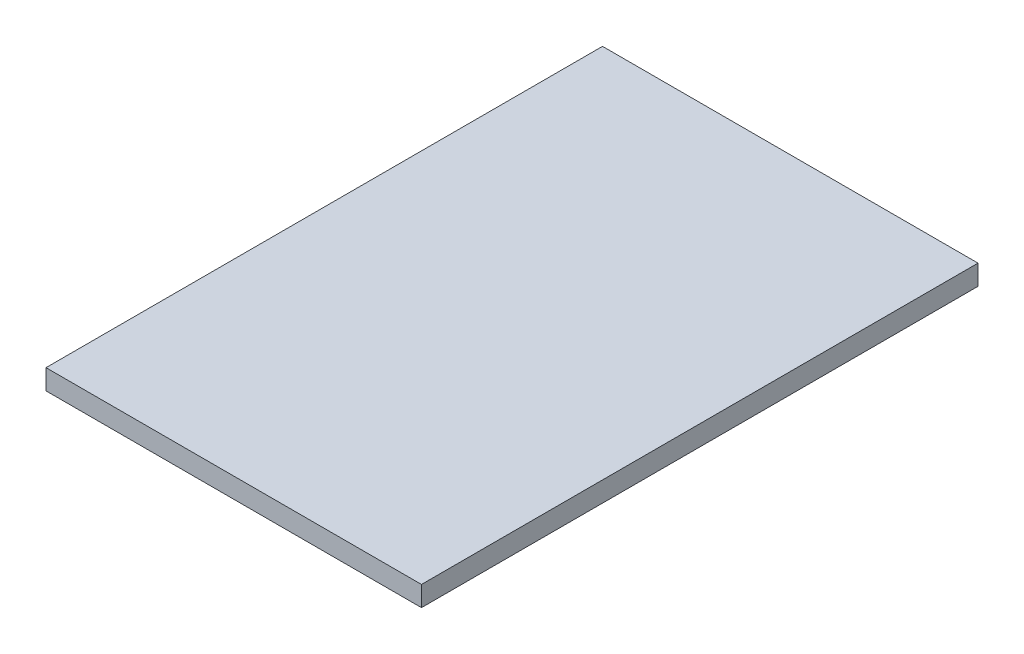
SolidWorks part; units mm, degrees
material "Balsa"
ref_plane "Front Plane" through (0, 0, 0) normal (0, 0, 1) x (1, 0, 0)
ref_plane "Top Plane" through (0, 0, 0) normal (0, 1, 0) x (1, 0, 0)
ref_plane "Right Plane" through (0, 0, 0) normal (1, 0, 0) x (0, 0, -1)
sketch "Sketch1" plane through (0, 0, 0) normal (0, 1, 0) x (1, 0, 0)
  line L1 (-88.9, -131.7625) -> (88.9, -131.7625)
  line L2 (-88.9, -131.7625) -> (-88.9, 131.7625)
  line L3 (-88.9, 131.7625) -> (88.9, 131.7625)
  line L4 (88.9, -131.7625) -> (88.9, 131.7625)
  line L5 (-88.9, -131.7625) -> (88.9, 131.7625) construction
  line L6 (-88.9, 131.7625) -> (88.9, -131.7625) construction
  point P0 (0, 0)
  dimension "D1" = 263.525
  dimension "D2" = 177.8
extrude "Boss-Extrude1" add sketch "Sketch1" along normal blind 9.525
